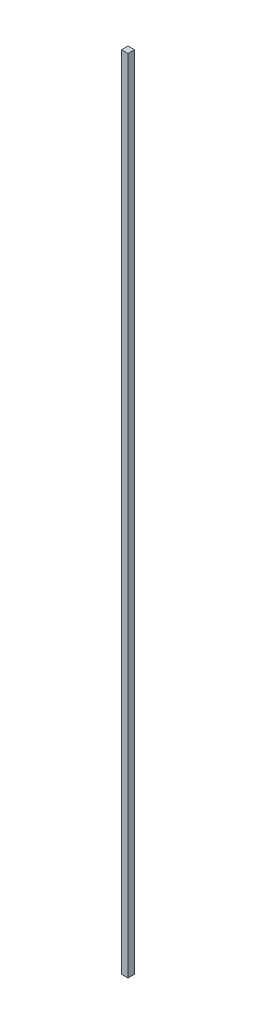
SolidWorks part; units mm, degrees
ref_plane "Front Plane" through (0, 0, 0) normal (0, 0, 1) x (1, 0, 0)
ref_plane "Top Plane" through (0, 0, 0) normal (0, 1, 0) x (1, 0, 0)
ref_plane "Right Plane" through (0, 0, 0) normal (1, 0, 0) x (0, 0, -1)
sketch "Sketch1" plane through (0, 0, 0) normal (0, 1, 0) x (1, 0, 0)
  line L1 (0, 0) -> (20, 0)
  line L2 (0, 0) -> (0, -20)
  line L3 (0, -20) -> (20, -20)
  line L4 (20, 0) -> (20, -20)
extrude "Boss-Extrude1" add sketch "Sketch1" along normal blind 2465
